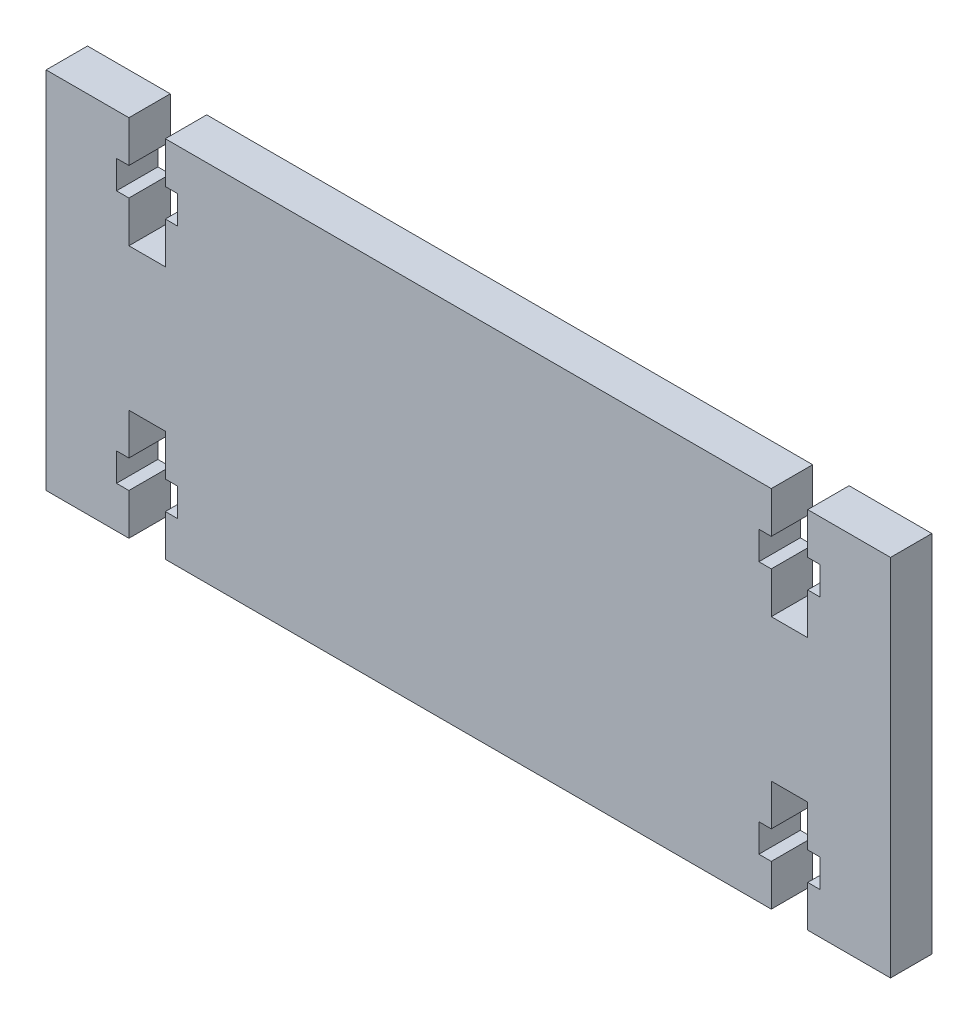
SolidWorks part; units mm, degrees
ref_plane "Front Plane" through (0, 0, 0) normal (0, 0, 1) x (1, 0, 0)
ref_plane "Top Plane" through (0, 0, 0) normal (0, 1, 0) x (1, 0, 0)
ref_plane "Right Plane" through (0, 0, 0) normal (1, 0, 0) x (0, 0, -1)
sketch "Sketch1" plane through (0, 0, 0) normal (0, 0, 1) x (1, 0, 0)
  line L1 (-51, 22) -> (51, 22)
  line L2 (-51, 22) -> (-51, -22)
  line L3 (-51, -22) -> (51, -22)
  line L4 (51, 22) -> (51, -22)
  dimension "D1" = 102
  dimension "D2" = 51
  dimension "D3" = 44
  dimension "D4" = 22
extrude "Boss-Extrude1" add sketch "Sketch1" along normal blind 5
sketch "Sketch3" plane through (0, 0, 5) normal (0, 0, 1) x (1, 0, 0)
  line L0 (-38.8, 1.3) -> (-38.8, 16.1452) construction
  line L1 (-36.6, 13.6) -> (-36.6, 8.6)
  line L2 (-41, 17) -> (-41, 22)
  line L3 (-35.1, 17) -> (-36.6, 17)
  line L4 (-35.1, 13.6) -> (-35.1, 17)
  line L5 (-36.6, 13.6) -> (-35.1, 13.6)
  line L6 (-42.5, 17) -> (-41, 17)
  line L7 (-42.5, 13.6) -> (-42.5, 17)
  line L8 (-41, 13.6) -> (-42.5, 13.6)
  line L9 (-41, 8.6) -> (-36.6, 8.6)
  line L10 (-36.6, 22) -> (-36.6, 17)
  line L11 (-41, 22) -> (-36.6, 22)
  line L12 (-41, 8.6) -> (-41, 13.6)
  line L14 (51, 22) -> (-51, 22) construction
  line L15 (-51, 22) -> (-51, -22) construction
  line L16 (0, 22) -> (0, -11.575) construction
  line L17 (51, 22) -> (-51, 22) construction
  line L18 (0, 0) -> (31.3946, 0) construction
  line L19 (38.8, 1.3) -> (38.8, 16.1452) construction
  line L20 (41, 8.6) -> (41, 13.6)
  line L21 (41, 22) -> (36.6, 22)
  line L22 (36.6, 22) -> (36.6, 17)
  line L23 (41, 8.6) -> (36.6, 8.6)
  line L24 (41, 13.6) -> (42.5, 13.6)
  line L25 (42.5, 13.6) -> (42.5, 17)
  line L26 (42.5, 17) -> (41, 17)
  line L27 (36.6, 13.6) -> (35.1, 13.6)
  line L28 (35.1, 13.6) -> (35.1, 17)
  line L29 (35.1, 17) -> (36.6, 17)
  line L30 (41, 17) -> (41, 22)
  line L31 (36.6, 13.6) -> (36.6, 8.6)
  line L32 (38.8, -1.3) -> (38.8, -16.1452) construction
  line L33 (36.6, -13.6) -> (36.6, -8.6)
  line L34 (41, -17) -> (41, -22)
  line L35 (35.1, -17) -> (36.6, -17)
  line L36 (35.1, -13.6) -> (35.1, -17)
  line L37 (36.6, -13.6) -> (35.1, -13.6)
  line L38 (42.5, -17) -> (41, -17)
  line L39 (42.5, -13.6) -> (42.5, -17)
  line L40 (41, -13.6) -> (42.5, -13.6)
  line L41 (41, -8.6) -> (36.6, -8.6)
  line L42 (36.6, -22) -> (36.6, -17)
  line L43 (41, -22) -> (36.6, -22)
  line L44 (41, -8.6) -> (41, -13.6)
  line L45 (-38.8, -1.3) -> (-38.8, -16.1452) construction
  line L46 (-41, -8.6) -> (-41, -13.6)
  line L47 (-41, -22) -> (-36.6, -22)
  line L48 (-36.6, -22) -> (-36.6, -17)
  line L49 (-41, -8.6) -> (-36.6, -8.6)
  line L50 (-41, -13.6) -> (-42.5, -13.6)
  line L51 (-42.5, -13.6) -> (-42.5, -17)
  line L52 (-42.5, -17) -> (-41, -17)
  line L53 (-36.6, -13.6) -> (-35.1, -13.6)
  line L54 (-35.1, -13.6) -> (-35.1, -17)
  line L55 (-35.1, -17) -> (-36.6, -17)
  line L56 (-41, -17) -> (-41, -22)
  line L57 (-36.6, -13.6) -> (-36.6, -8.6)
  dimension "D1" = 5
  dimension "D2" = 3.4
  dimension "D3" = 5
  dimension "D4" = 2.2
  dimension "D5" = 4.4
  dimension "D6" = 1.5
  dimension "D7" = 1.5
  dimension "D8" = 10
extrude "Cut-Extrude1" cut sketch "Sketch3" against normal blind 5
